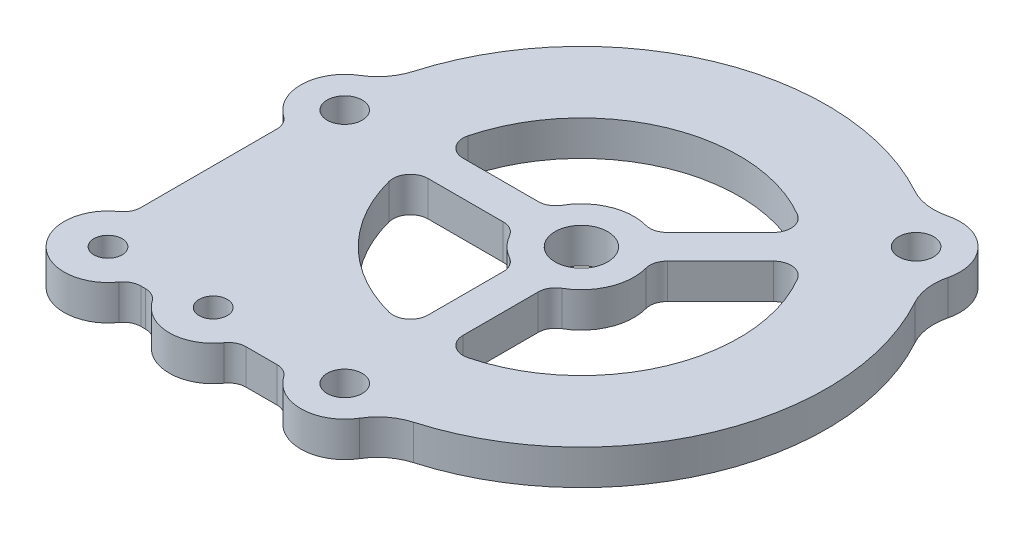
SolidWorks part; units mm, degrees
material "5052-H32"
ref_plane "Front Plane" through (0, 0, 0) normal (0, 0, 1) x (1, 0, 0)
ref_plane "Top Plane" through (0, 0, 0) normal (0, 1, 0) x (1, 0, 0)
ref_plane "Right Plane" through (0, 0, 0) normal (1, 0, 0) x (0, 0, -1)
sketch "Sketch1" plane through (0, 0, 0) normal (0, 1, 0) x (1, 0, 0)
  arc A0 (-42.7069, -12.3258) -> (-12.3258, -42.7069) centre (0, 0) ccw
  circle A1 centre (0, 0) radius 42.8625 construction
  arc A2 (-46.9515, 6.8032) -> (-46.9515, -6.8032) centre (-42.8625, 0) ccw
  arc A3 (-6.8032, -46.9515) -> (6.8032, -46.9515) centre (0, -42.8625) ccw
  arc A4 (38.0103, 28.3891) -> (28.3891, 38.0103) centre (30.3084, 30.3084) ccw
  arc A5 (21.4826, 38.914) -> (-42.7069, 12.3258) centre (0, 0) ccw
  arc A6 (12.3258, -42.7069) -> (38.914, 21.4826) centre (0, 0) ccw
  arc A7 (28.3891, 38.0103) -> (21.4826, 38.914) centre (26.086, 47.2527) cw
  arc A8 (38.0103, 28.3891) -> (38.914, 21.4826) centre (47.2527, 26.086) ccw
  arc A9 (12.3258, -42.7069) -> (6.8032, -46.9515) centre (14.9671, -51.8583) ccw
  arc A10 (-6.8032, -46.9515) -> (-12.3258, -42.7069) centre (-14.9671, -51.8583) ccw
  arc A11 (-42.7069, -12.3258) -> (-46.9515, -6.8032) centre (-51.8583, -14.9671) ccw
  arc A12 (-42.7069, 12.3258) -> (-46.9515, 6.8032) centre (-51.8583, 14.9671) cw
  point P14 (25.3541, 36.5099)
  point P19 (7.8884, -43.7444)
  dimension "D1" = 88.9
  dimension "D2" = 85.725
  dimension "D5" = 15.875
  dimension "D6" = 9.525
  dimension "D3" = 135
  dimension "D4" = 90
extrude "Boss-Extrude1" add sketch "Sketch1" along normal blind 6.35
sketch "Sketch2" plane through (0, 6.35, 0) normal (0, 1, 0) x (1, 0, 0)
  circle A0 centre (0, 0) radius 4.7625
  dimension "D1" = 9.525
extrude "Cut-Extrude1" cut sketch "Sketch2" against normal through all
hole_wizard "1/4 (0.25) Diameter Hole1" positions "Sketch3" profile "Sketch4" hole size "1/4" standard "ANSI Inch" end condition through all
sketch "Sketch3" plane through (0, 6.35, 0) normal (0, 1, 0) x (1, 0, 0)
  point P0 (-42.8625, 0)
  point P3 (30.3084, 30.3084)
  point P6 (0, -42.8625)
sketch "Sketch4" plane through (-42.8625, 6.35, 0) normal (1, 0, 0) x (0, 0, 1)
  line L0 (0, 0) -> (0, 6.35)
  line L1 (0, 6.35) -> (3.175, 6.35)
  line L2 (3.175, 6.35) -> (3.175, 0)
  line L5 (3.175, 0) -> (0, 0)
  line L11 (0, -6.35) -> (0, 107.95) construction
  dimension "Thru Hole Dia." = 6.35
  dimension "Thru Hole Depth" = 6.35
sketch "Sketch5" plane through (0, 6.35, 0) normal (0, 1, 0) x (1, 0, 0)
  line L2 (-28.3981, 3.175) -> (-8.9803, 3.175)
  line L3 (-28.3981, -3.175) -> (-8.9803, -3.175)
  line L4 (22.3255, 17.8354) -> (8.5951, 4.1049)
  line L5 (17.8354, 22.3255) -> (4.1049, 8.5951)
  line L6 (-3.175, -28.3981) -> (-3.175, -8.9803)
  line L7 (3.175, -28.3981) -> (3.175, -8.9803)
  line L8 (0, 0) -> (0, -42.8625) construction
  line L9 (0, 0) -> (30.3084, 30.3084) construction
  arc A3 (-8.9803, -3.175) -> (-3.175, -8.9803) centre (0, 0) ccw
  arc A4 (-28.3981, -3.175) -> (-3.175, -28.3981) centre (0, 0) ccw
  circle A5 centre (0, 0) radius 4.7625 construction
  arc A6 (3.175, -28.3981) -> (22.3255, 17.8354) centre (0, 0) ccw
  arc A7 (3.175, -8.9803) -> (8.5951, 4.1049) centre (0, 0) ccw
  arc A8 (17.8354, 22.3255) -> (-28.3981, 3.175) centre (0, 0) ccw
  arc A9 (4.1049, 8.5951) -> (-8.9803, 3.175) centre (0, 0) ccw
  point P21 (0, 0)
  dimension "D1" = 57.15
  dimension "D2" = 4.7625
  dimension "D3" = 6.35
  dimension "D4" = 6.35
  dimension "D5" = 6.35
extrude "Cut-Extrude2" cut sketch "Sketch5" against normal through all
fillet "Fillet1" radius 3.175 12 edges at (3.175, 3.175, 28.3981) (-3.175, 3.175, 28.3981) (-28.3981, 3.175, 3.175) (-8.9803, 3.175, 3.175) (-3.175, 3.175, 8.9803) (3.175, 3.175, 8.9803) (8.5951, 3.175, -4.1049) (22.3255, 3.175, -17.8354) (17.8354, 3.175, -22.3255) (4.1049, 3.175, -8.5951) (-8.9803, 3.175, -3.175) (-28.3981, 3.175, -3.175)
sketch "Sketch8" plane through (0, 6.35, 0) normal (0, 1, 0) x (1, 0, 0)
  line L0 (-50.8, 0) -> (-50.8, -42.8625)
  line L1 (-42.8625, -50.8) -> (0, -50.8)
  arc A0 (-46.9515, 6.8032) -> (-46.9515, -6.8032) centre (-42.8625, 0) ccw construction
  arc A1 (-6.8032, -46.9515) -> (6.8032, -46.9515) centre (0, -42.8625) ccw construction
  arc A2 (-42.8625, -50.8) -> (-50.8, -42.8625) centre (-42.8625, -42.8625) cw
  arc A3 (-6.8032, -46.9515) -> (-12.3258, -42.7069) centre (-14.9671, -51.8583) ccw construction
  arc A4 (-42.7069, -12.3258) -> (-12.3258, -42.7069) centre (0, 0) ccw construction
  arc A5 (-42.7069, -12.3258) -> (-46.9515, -6.8032) centre (-51.8583, -14.9671) ccw construction
  arc A6 (-6.8032, -46.9515) -> (0, -50.8) centre (0, -42.8625) ccw
  arc A7 (-6.8032, -46.9515) -> (-12.3258, -42.7069) centre (-14.9671, -51.8583) ccw
  arc A8 (-42.7069, -12.3258) -> (-12.3258, -42.7069) centre (0, 0) ccw
  arc A9 (-42.7069, -12.3258) -> (-46.9515, -6.8032) centre (-51.8583, -14.9671) ccw
  arc A10 (-50.8, 0) -> (-46.9515, -6.8032) centre (-42.8625, 0) ccw
  dimension "D1" = 7.9375
extrude "Boss-Extrude2" add sketch "Sketch8" against normal up to surface (6.35 mm away) up to face at (11.5863, 0, 4.7992)
hole_wizard "#10 Clearance Hole1" positions "Sketch10" profile "Sketch11" hole size "#10" standard "ANSI Inch" end condition through all
sketch "Sketch10" plane through (0, 6.35, 0) normal (0, 1, 0) x (1, 0, 0)
  line L0 (-34.925, 0) -> (-31.75, 0)
  line L2 (-33.3375, 0) -> (-33.3375, -42.8625)
  line L4 (-42.8625, -42.8625) -> (-23.8125, -42.8625)
  circle A0 centre (0, 0) radius 31.75
  circle A1 centre (-42.8625, 0) radius 7.9375
  point P0 (-42.8625, -42.8625)
  point P3 (-23.8125, -42.8625)
  point P24 (-33.3375, -42.8625)
  dimension "D1" = 15.875
  dimension "D2" = 63.5
sketch "Sketch11" plane through (-42.8625, 6.35, 42.8625) normal (1, 0, 0) x (0, 0, 1)
  line L0 (0, 0) -> (0, 6.35)
  line L1 (0, 6.35) -> (2.5527, 6.35)
  line L2 (2.5527, 6.35) -> (2.5527, 0)
  line L5 (2.5527, 0) -> (0, 0)
  line L11 (0, -6.35) -> (0, 107.95) construction
  dimension "Thru Hole Dia." = 5.1054
  dimension "Thru Hole Depth" = 6.35
sketch "Sketch15" plane through (0, 6.35, 0) normal (0, 1, 0) x (1, 0, 0)
  line L0 (-46.0375, -7.2748) -> (-46.0375, -35.5877)
  line L1 (-35.5877, -46.0375) -> (-31.0873, -46.0375)
  line L2 (-16.5377, -46.0375) -> (-7.2748, -46.0375)
  line L3 (-50.8, 0) -> (-50.8, -42.8625) construction
  line L4 (-42.8625, -50.8) -> (0, -50.8) construction
  line L5 (-50.8, 0) -> (-50.8, -42.8625)
  line L6 (-42.8625, -50.8) -> (-23.8125, -50.8)
  line L7 (-23.8125, -50.8) -> (0, -50.8)
  line L8 (-39.6875, -7.2748) -> (-39.6875, -35.5877)
  line L9 (-35.5877, -39.6875) -> (-31.0873, -39.6875)
  arc A0 (-50.8, 0) -> (-46.0375, -7.2748) centre (-42.8625, 0) ccw
  arc A1 (-46.0375, -35.5877) -> (-50.8, -42.8625) centre (-42.8625, -42.8625) ccw
  arc A2 (-31.0873, -46.0375) -> (-23.8125, -50.8) centre (-23.8125, -42.8625) ccw
  arc A3 (-7.2748, -46.0375) -> (0, -50.8) centre (0, -42.8625) ccw
  arc A4 (-23.8125, -50.8) -> (-16.5377, -46.0375) centre (-23.8125, -42.8625) ccw
  arc A5 (-42.8625, -50.8) -> (-35.5877, -46.0375) centre (-42.8625, -42.8625) ccw
  arc A6 (-39.6875, -35.5877) -> (-35.5877, -39.6875) centre (-42.8625, -42.8625) cw
  arc A7 (-31.0873, -39.6875) -> (-26.7598, -35.4925) centre (-23.8125, -42.8625) cw
  arc A8 (-39.6875, -7.2748) -> (-43.7444, -7.8884) centre (-42.8625, 0) ccw
  arc A9 (-43.7444, -7.8884) -> (-26.7598, -35.4925) centre (0, 0) ccw
  arc A12 (21.4826, 38.914) -> (-42.7069, 12.3258) centre (0, 0) ccw construction
  point P24 (-33.3375, -46.0375)
  line M13 (-42.8625, -50.8) -> (0, -50.8)
  line M23 (-50.8, 0) -> (-50.8, -42.8625)
  dimension "D1" = 3.175
  dimension "D2" = 3.175
  dimension "D3" = 6.35
  dimension "D4" = 6.35
extrude "Cut-Extrude5" cut sketch "Sketch15" against normal blind 6.35 contours A1 L0 A0 M23 | A5 A2 L1 M13 | A4 A3 L2 M13
fillet "Fillet3" radius 3.175 6 edges at (-7.2748, 3.175, 46.0375) (-16.5377, 3.175, 46.0375) (-46.0375, 3.175, 35.5877) (-46.0375, 3.175, 7.2748) (-31.0873, 3.175, 46.0375) (-35.5877, 3.175, 46.0375)
